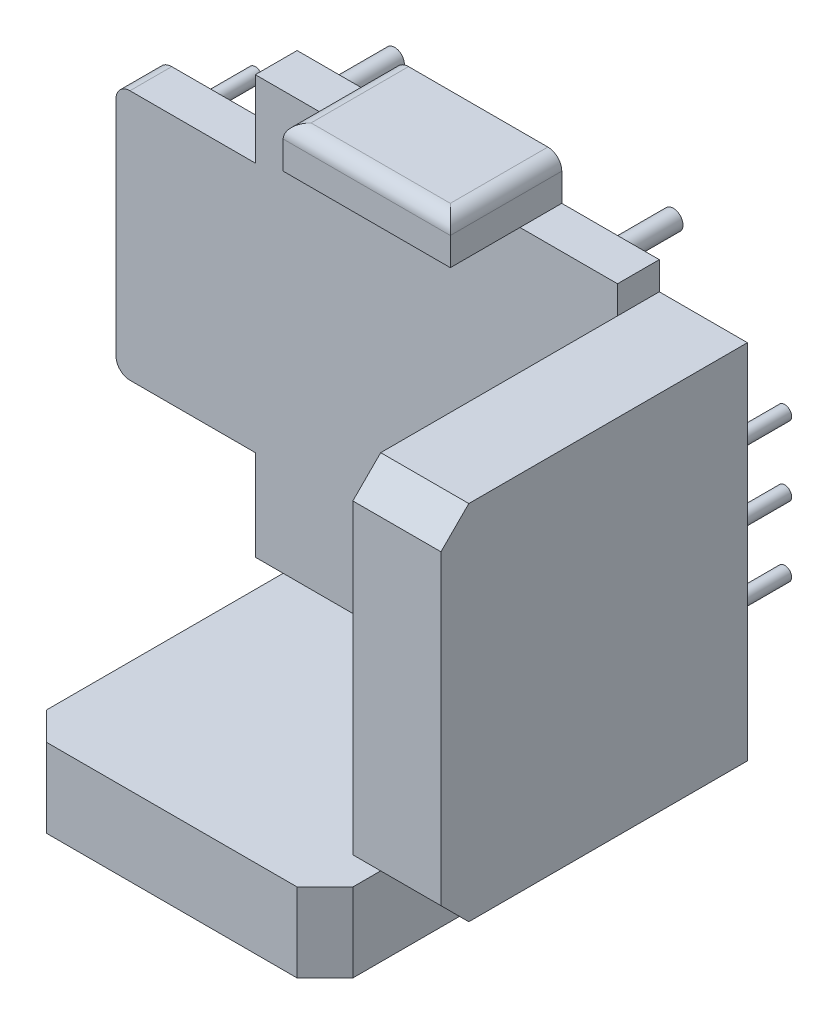
SolidWorks part; units mm, degrees
ref_plane "Plano frontal" through (0, 0, 0) normal (0, 0, 1) x (1, 0, 0)
ref_plane "Plano superior" through (0, 0, 0) normal (0, 1, 0) x (1, 0, 0)
ref_plane "Plano direito" through (0, 0, 0) normal (1, 0, 0) x (0, 0, -1)
sketch "Esboço3" plane through (0, 0, 0) normal (0, 0, -1) x (-1, 0, 0)
  line L5 (11.5, 4.75) -> (6.5, 4.75)
  line L11 (11.5, -4.25) -> (11.5, 4.75)
  line L25 (-6.65, -6.65) -> (-6.65, 6.65) construction
  line L32 (6.65, -6.65) -> (-6.65, -6.65) construction
  line L53 (-6.5, -7.5) -> (-5.5, -7.5)
  line L54 (-6.5, -7.5) -> (-6.5, -6.5)
  line L55 (-6.5, 7.5) -> (6.5, 7.5)
  line L56 (6.5, -7.5) -> (6.5, -4.25)
  line L57 (-6.5, -7.5) -> (6.5, 7.5) construction
  line L58 (-6.5, 7.5) -> (6.5, -7.5) construction
  line L59 (11.5, -4.25) -> (6.5, -4.25)
  line L60 (5.5, -7.5) -> (5.5, -9.5)
  line L61 (5.5, -9.5) -> (4, -9.5)
  line L62 (4, -9.5) -> (4, -7.5)
  line L63 (0, -7.5) -> (0, 7.5) construction
  line L64 (6.5, 0) -> (-6.5, 0) construction
  line L65 (-4, -9.5) -> (-4, -7.5)
  line L66 (-5.5, -9.5) -> (-4, -9.5)
  line L67 (-5.5, -7.5) -> (-5.5, -9.5)
  line L68 (-6.5, -6.5) -> (-8.5, -6.5)
  line L69 (-8.5, -6.5) -> (-8.5, -5)
  line L70 (-8.5, -5) -> (-6.5, -5)
  line L71 (-8.5, 5) -> (-6.5, 5)
  line L72 (-8.5, 6.5) -> (-8.5, 5)
  line L73 (-6.5, 6.5) -> (-8.5, 6.5)
  line L74 (-6.5, 6.5) -> (-6.5, 7.5)
  line L75 (-6.5, -5) -> (-6.5, 5)
  line L76 (-4, -7.5) -> (4, -7.5)
  line L77 (5.5, -7.5) -> (6.5, -7.5)
  line L78 (6.5, 4.75) -> (6.5, 7.5)
  point P0 (0, 0)
  dimension "D1" = 7.5
  dimension "D2" = 9
  dimension "D3" = 4.75
  dimension "D4" = 1.5
  dimension "D5" = 6.5
  dimension "D6" = 2
  dimension "D7" = 1
  dimension "D8" = 1.5
  dimension "D9" = 2
  dimension "D10" = 6.5
  dimension "D11" = 5
  dimension "D12" = 1
extrude "Ressalto-extrusão4" add sketch "Esboço3" along normal blind 1.5
sketch "Esboço5" plane through (0, 0, -1.5) normal (0, 0, -1) x (-1, 0, 0)
  line L0 (0, 0) -> (0, 8.25) construction
  line L6 (6.5, 7.5) -> (-6.5, 7.5) construction
  line L7 (-3, 9) -> (3, 9)
  line L9 (-3, 9) -> (-3, 7.5)
  line L10 (-3, 7.5) -> (3, 7.5)
  line L11 (3, 9) -> (3, 7.5)
  line L12 (-3, 9) -> (3, 7.5) construction
  line L13 (-3, 7.5) -> (3, 9) construction
  dimension "D1" = 1.5
  dimension "D2" = 6
extrude "Ressalto-extrusão6" add sketch "Esboço5" against normal blind 4
sketch "Esboço6" plane through (0, 0, -1.5) normal (0, 0, -1) x (-1, 0, 0)
  line L12 (0, 0) -> (0, -10.3298) construction
  line L13 (-6.5, 4.99) -> (-8.51, 4.99)
  line L24 (-4, -9.5) -> (-4, -7.5) construction
  line L25 (-5.5, -9.5) -> (-4, -9.5) construction
  line L26 (4, -7.5) -> (4, -9.5) construction
  line L27 (4, -9.5) -> (5.5, -9.5) construction
  line L28 (-3.99, -7.5) -> (-3.99, -9.51)
  line L29 (-4, -7.5) -> (4, -7.5) construction
  line L30 (-3.99, -9.51) -> (-5.5, -9.51)
  line L31 (-5.5, -9.51) -> (-5.5, -10.3298)
  line L32 (-5.5, -10.3298) -> (5.5, -10.3298)
  line L33 (5.5, -10.3298) -> (5.5, -9.51)
  line L34 (5.5, -9.51) -> (3.99, -9.51)
  line L35 (3.99, -9.51) -> (3.99, -7.5)
  line L36 (3.99, -7.5) -> (-3.99, -7.5)
  line L37 (-6.5, 5) -> (-6.5, -5) construction
  line L38 (-8.51, 4.99) -> (-8.51, 6.5)
  line L39 (-8.51, 6.5) -> (-9.6631, 6.5)
  line L40 (-9.6631, 6.5) -> (-9.6631, -6.5)
  line L41 (-9.6631, -6.5) -> (-8.51, -6.5)
  line L42 (-8.51, -6.5) -> (-8.51, -4.99)
  line L43 (-8.51, -4.99) -> (-6.5, -4.99)
  line L44 (-6.5, -4.99) -> (-6.5, 4.99)
  line L45 (-6.5, -5) -> (-8.5, -5) construction
  line L46 (-8.5, -5) -> (-8.5, -6.5) construction
  line L47 (-8.5, 5) -> (-6.5, 5) construction
  line L48 (-8.5, 6.5) -> (-8.5, 5) construction
  line L49 (0, 0) -> (-9.6631, 0) construction
  point P18 (0, 0)
  point P21 (0, 0)
  point P34 (0, -10.3298)
  point P43 (0, 0)
  point P44 (0, 0)
  dimension "D2" = 0.01
  dimension "D3" = 0.01
  dimension "D4" = 0.01
  dimension "D5" = 0.01
  dimension "D6" = 13
  dimension "D7" = 11
  dimension "D8" = 0.01
  dimension "D9" = 0.01
  dimension "D10" = 0.01
  dimension "D11" = 0.01
extrude "Ressalto-extrusão7" add sketch "Esboço6" against normal blind 11
sketch "Esboço8" plane through (0, 0, 9.5) normal (0, 0, 1) x (1, 0, 0)
  line L5 (8.51, -6.5) -> (6.5, -6.5)
  line L6 (8.5, -6.5) -> (6.5, -6.5) construction
  line L7 (6.5, -6.5) -> (6.5, -4.99)
  line L8 (6.5, -4.99) -> (8.51, -4.99)
  line L9 (8.51, -4.99) -> (8.51, -6.5)
  line L10 (0, 0) -> (9.6631, 0) construction
  line L11 (9.6631, 6.5) -> (9.6631, -6.5) construction
  line L12 (8.51, 4.99) -> (8.51, 6.5)
  line L13 (6.5, 4.99) -> (8.51, 4.99)
  line L14 (6.5, 6.5) -> (6.5, 4.99)
  line L15 (8.51, 6.5) -> (6.5, 6.5)
extrude "Ressalto-extrusão15" add sketch "Esboço8" against normal blind 11
sketch "Esboço9" plane through (0, 0, 9.5) normal (0, 0, 1) x (1, 0, 0)
  line L10 (-5.5, -9.51) -> (-3.99, -9.51)
  line L11 (-3.99, -9.51) -> (-3.99, -7.5)
  line L12 (-3.99, -7.5) -> (-5.5, -7.5)
  line L13 (-5.5, -7.5) -> (-5.5, -9.51)
  line L14 (0, 0) -> (0, -10.3298) construction
  line L15 (5.5, -10.3298) -> (-5.5, -10.3298) construction
  line L16 (5.5, -7.5) -> (5.5, -9.51)
  line L17 (3.99, -7.5) -> (5.5, -7.5)
  line L18 (3.99, -9.51) -> (3.99, -7.5)
  line L19 (5.5, -9.51) -> (3.99, -9.51)
extrude "Ressalto-extrusão16" add sketch "Esboço9" against normal blind 11
sketch "Esboço10" plane through (0, 0, -1.5) normal (0, 0, -1) x (-1, 0, 0)
  line L0 (11.5, 4.75) -> (6.5, 4.75) construction
  line L1 (11.5, -4.25) -> (11.5, 4.75) construction
  line L3 (6.5, -4.25) -> (11.5, -4.25) construction
  circle A0 centre (10.5, 3.5) radius 0.25
  circle A1 centre (6.5, 3.5) radius 0.25
  circle A2 centre (10.5, -3) radius 0.25
  circle A3 centre (6.5, -3) radius 0.25
  dimension "D1" = 0.5
  dimension "D9" = 1.25
  dimension "D8" = 4
  dimension "D2" = 1.25
  dimension "D3" = 1.25
  dimension "D4" = 1
  dimension "D5" = 4
  dimension "D6" = 6.5
  dimension "D7" = 1
extrude "Ressalto-extrusão17" add sketch "Esboço10" along normal blind 2.5
sketch "Esboço11" plane through (0, 0, 0) normal (0, 0, 1) x (1, 0, 0)
  circle A0 centre (-5.5, 6.5) radius 0.35
  circle A1 centre (4.5, 6.5) radius 0.35
  circle A2 centre (4.5, -6.5) radius 0.35
  circle A3 centre (-5.5, -6.5) radius 0.35
  dimension "D1" = 0.7
extrude "Ressalto-extrusão18" add sketch "Esboço11" against normal blind 4
sketch "Esboço12" plane through (0, 0, -1.5) normal (0, 0, -1) x (-1, 0, 0)
  circle A0 centre (3, -8.5) radius 0.25
  circle A1 centre (0.5, -8.5) radius 0.25
  circle A2 centre (-2, -8.5) radius 0.25
  circle A3 centre (-8.5, -2.5) radius 0.25
  circle A4 centre (-8.5, 0) radius 0.25
  circle A5 centre (-8.5, 2.5) radius 0.25
  dimension "D1" = 0.5
extrude "Ressalto-extrusão19" add sketch "Esboço12" along normal blind 2.5
chamfer "Chanfro1" distance 1 angle 45 4 edges at (8.0816, 6.5, 9.5) (8.0816, -6.5, 9.5) (5.5, -8.9149, 9.5) (-5.5, -8.9149, 9.5)
fillet "Filete2" radius 0.5 5 edges at (-11.5, 4.75, -0.75) (-11.5, -4.25, -0.75) (3, 9, 0.5) (0, 9, 2.5) (-3, 9, 0.5)
